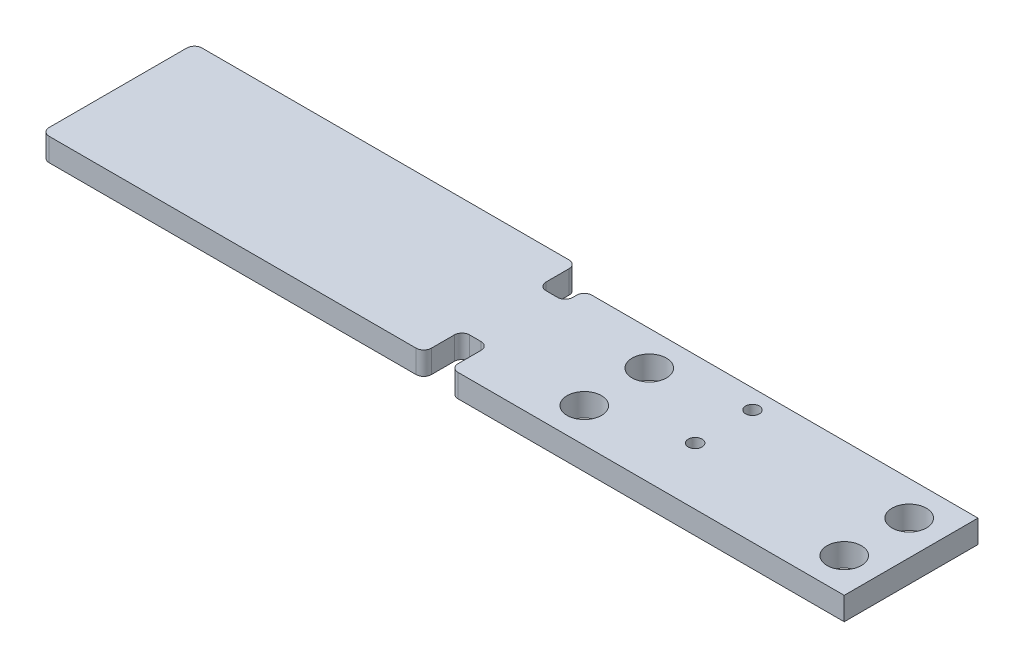
SolidWorks part; units mm, degrees
material "2014 合金"
ref_plane "前视基准面" through (0, 0, 0) normal (0, 0, 1) x (1, 0, 0)
ref_plane "上视基准面" through (0, 0, 0) normal (0, 1, 0) x (1, 0, 0)
ref_plane "右视基准面" through (0, 0, 0) normal (1, 0, 0) x (0, 0, -1)
sketch "草图4" plane through (0, 0, 0) normal (0, 1, 0) x (1, 0, 0)
  line L0 (136.4611, 47.1597) -> (136.4611, 22.1597)
  line L1 (-71.5389, 52.1597) -> (24.4611, 52.1597)
  line L2 (-73.5389, 50.1597) -> (-73.5389, 14.1597)
  line L3 (-71.5389, 12.1597) -> (24.4611, 12.1597)
  line L5 (136.4611, 47.1597) -> (35.4611, 47.1597)
  line L8 (26.4611, 49.7444) -> (26.4611, 50.1597)
  line L12 (26.4611, 20.1713) -> (26.4611, 14.1597)
  line L16 (26.4611, 49.7444) -> (26.4611, 44.1597)
  line L17 (28.4611, 42.1597) -> (31.4611, 42.1597)
  line L18 (33.4611, 44.1597) -> (33.4611, 45.1597)
  line L19 (28.4494, 22.1597) -> (31.4611, 22.1597)
  line L20 (33.4611, 20.1597) -> (33.4611, 14.1597)
  line L21 (35.4611, 12.1597) -> (136.4611, 12.1597)
  line L22 (136.4611, 12.1597) -> (136.4611, 22.1597)
  arc A0 (-71.5389, 52.1597) -> (-73.5389, 50.1597) centre (-71.5389, 50.1597) ccw
  arc A1 (-73.5389, 14.1597) -> (-71.5389, 12.1597) centre (-71.5389, 14.1597) ccw
  arc A3 (28.4494, 22.1597) -> (26.4611, 20.1713) centre (28.4494, 20.1713) ccw
  arc A4 (24.4611, 12.1597) -> (26.4611, 14.1597) centre (24.4611, 14.1597) ccw
  arc A5 (26.4611, 50.1597) -> (24.4611, 52.1597) centre (24.4611, 50.1597) ccw
  arc A6 (35.4611, 47.1597) -> (33.4611, 45.1597) centre (35.4611, 45.1597) ccw
  arc A7 (31.4611, 42.1597) -> (33.4611, 44.1597) centre (31.4611, 44.1597) ccw
  arc A8 (26.4611, 44.1597) -> (28.4611, 42.1597) centre (28.4611, 44.1597) ccw
  circle A9 centre (82.4611, 27.1597) radius 1.8
  circle A10 centre (82.4611, 42.1597) radius 1.8
  arc A11 (33.4611, 14.1597) -> (35.4611, 12.1597) centre (35.4611, 14.1597) ccw
  arc A12 (31.4611, 22.1597) -> (33.4611, 20.1597) centre (31.4611, 20.1597) cw
  circle A13 centre (59.4611, 38.1597) radius 4.5
  circle A14 centre (59.4611, 21.1597) radius 4.5
  circle A15 centre (127.4611, 38.1597) radius 4.5
  circle A16 centre (127.4611, 21.1597) radius 4.5
  point P8 (33.4611, 47.1597)
  point P12 (-73.5389, 52.1597)
  point P15 (-73.5389, 12.1597)
  point P18 (26.4611, 47.1597)
  point P21 (26.4611, 22.1597)
  point P30 (33.4611, 42.1597)
  point P33 (26.4611, 42.1597)
  point P49 (0, 0)
  dimension "D7" = 2
  dimension "D4" = 2
  dimension "D10" = 2
  dimension "D11" = 3.6
  dimension "D12" = 3.6
  dimension "D17" = 2
  dimension "D18" = 9
  dimension "D19" = 26
  dimension "D20" = 9
  dimension "D21" = 9
  dimension "D25" = 9
  dimension "D1" = 100
  dimension "D2" = 40
  dimension "D3" = 110
  dimension "D5" = 25
  dimension "D6" = 5
  dimension "D8" = 7
  dimension "D9" = 5
  dimension "D13" = 5
  dimension "D14" = 15
  dimension "D15" = 56
  dimension "D16" = 56
  dimension "D22" = 33
  dimension "D23" = 33
  dimension "D24" = 10
  dimension "D26" = 17
  dimension "D27" = 9
extrude "凸台-拉伸1" add sketch "草图4" along normal blind 6
